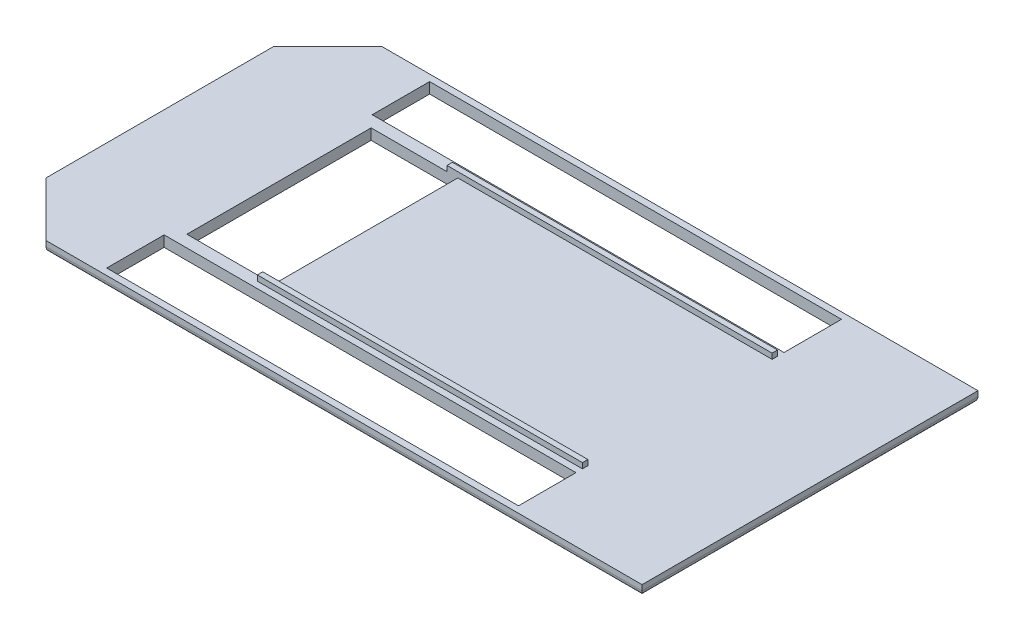
SolidWorks part; units mm, degrees
ref_plane "Front Plane" through (0, 0, 0) normal (0, 0, 1) x (1, 0, 0)
ref_plane "Top Plane" through (0, 0, 0) normal (0, 1, 0) x (1, 0, 0)
ref_plane "Right Plane" through (0, 0, 0) normal (1, 0, 0) x (0, 0, -1)
sketch "Sketch1" plane through (0, 0, 0) normal (0, 1, 0) x (1, 0, 0)
  line L0 (-300, 105) -> (-250, 155)
  line L1 (-250, 155) -> (300, 155)
  line L2 (-300, 105) -> (-300, -105)
  line L3 (-250, -155) -> (300, -155)
  line L4 (300, 155) -> (300, -155)
  line L5 (-255.799, 169) -> (314, 169) construction
  line L6 (314, 169) -> (314, -169) construction
  line L7 (-55, 0) -> (55, 0) construction
  line L8 (-300, -105) -> (-250, -155)
  line L9 (-255.799, -169) -> (314, -169) construction
  line L10 (-314, -110.799) -> (-255.799, -169) construction
  line L11 (-314, 110.799) -> (-314, -110.799) construction
  line L12 (-314, 110.799) -> (-255.799, 169) construction
  point P0 (0, 0)
  dimension "D1" = 14
  dimension "D2" = 310
  dimension "D3" = 50
  dimension "D4" = 50
extrude "Boss-Extrude2" add sketch "Sketch1" along normal blind 10
sketch "Sketch2" plane through (0, 10, 0) normal (0, 1, 0) x (1, 0, 0)
  line L0 (180, 155) -> (180, -155) construction
  line L1 (300, 155) -> (-250, 155) construction
  line L2 (-250, -155) -> (300, -155) construction
  line L3 (300, -155) -> (300, 155) construction
  line L4 (-312.4805, 0) -> (306.6914, 0) construction
  line L5 (-120, -85) -> (180, -85)
  line L6 (-120, 85) -> (180, 85)
  line L7 (-120, 85) -> (-120, 90)
  line L8 (-120, 90) -> (180, 90)
  line L9 (180, 90) -> (180, 85)
  line L10 (-120, -85) -> (-120, -90)
  line L11 (-120, -90) -> (180, -90)
  line L12 (180, -90) -> (180, -85)
  dimension "D1" = 120
  dimension "D4" = 85
  dimension "D2" = 300
  dimension "D3" = 170
  dimension "D5" = 5
  dimension "D6" = 5
extrude "Boss-Extrude3" add sketch "Sketch2" along normal blind 5
fillet "Fillet1" radius 5 6 edges at (25, 0, -155) (-275, 0, -130) (-300, 0, 0) (-275, 0, 130) (25, 0, 155) (300, 0, 0)
sketch "Sketch3" plane through (0, 10, 0) normal (0, 1, 0) x (1, 0, 0)
  line L0 (180, -161.5513) -> (180, -90) construction
  line L5 (180, 149) -> (-200, 149)
  line L6 (-200, 96) -> (-200, 149)
  line L7 (180, 96) -> (-200, 96)
  line L8 (180, 96) -> (180, 149)
  line L9 (180, -90) -> (180, 174.2238) construction
  line L10 (300, 155) -> (-250, 155) construction
  line L11 (180, 90) -> (-120, 90) construction
  line L12 (-8.25, 0) -> (8.25, 0) construction
  line L13 (180, -96) -> (180, -149)
  line L14 (180, -96) -> (-200, -96)
  line L15 (-200, -96) -> (-200, -149)
  line L16 (180, -149) -> (-200, -149)
  line L18 (-190, 85) -> (-110, 85)
  line L19 (-190, 85) -> (-190, -85)
  line L20 (-190, -85) -> (-110, -85)
  line L21 (-110, 85) -> (-110, -85)
  point P22 (-110, 0)
  point P24 (0, 0)
  dimension "D1" = 380
  dimension "D2" = 6
  dimension "D3" = 6
  dimension "D4" = 170
  dimension "D5" = 80
  dimension "D6" = 10
extrude "Cut-Extrude1" cut sketch "Sketch3" against normal blind 10
